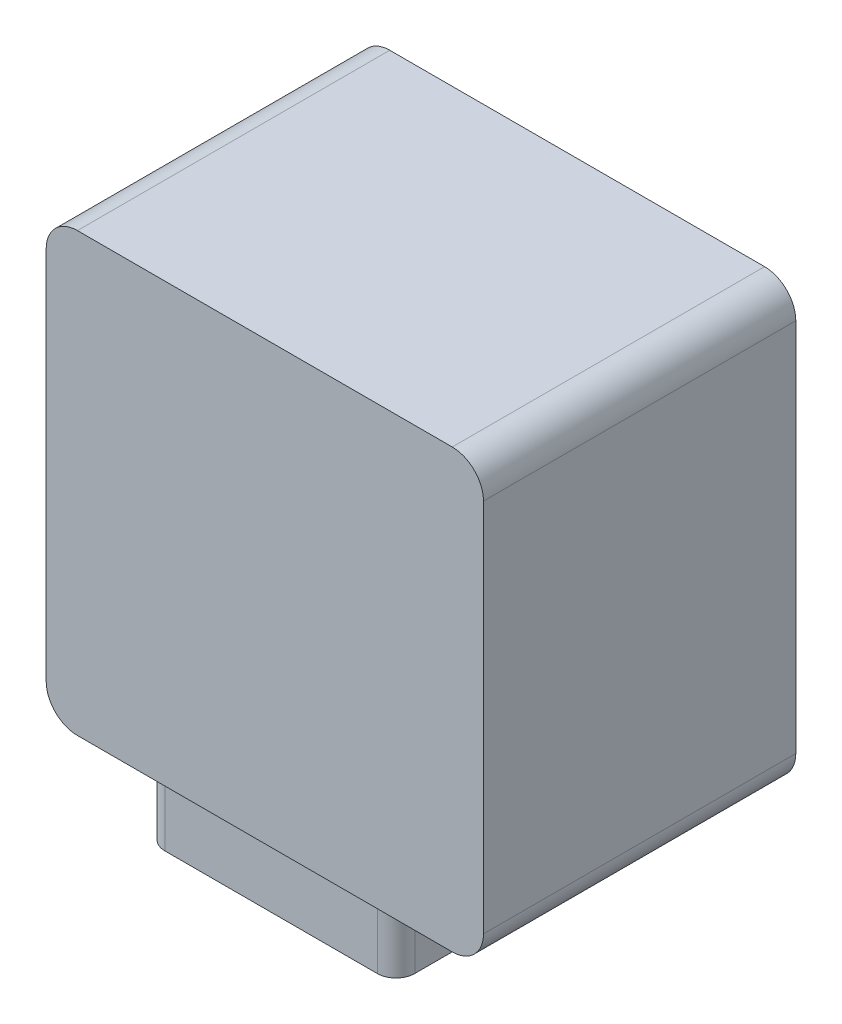
SolidWorks part; units mm, degrees
ref_plane "前视基准面" through (0, 0, 0) normal (0, 0, 1) x (1, 0, 0)
ref_plane "上视基准面" through (0, 0, 0) normal (0, 1, 0) x (1, 0, 0)
ref_plane "右视基准面" through (0, 0, 0) normal (1, 0, 0) x (0, 0, -1)
sketch "草图1" plane through (0, 0, 0) normal (0, 0, 1) x (1, 0, 0)
  line L1 (-48.1935, 66.2876) -> (11.8065, 66.2876)
  line L2 (-53.1935, 61.2876) -> (-53.1935, 1.2876)
  line L3 (-48.1935, -3.7124) -> (11.8065, -3.7124)
  line L4 (16.8065, 61.2876) -> (16.8065, 1.2876)
  line L5 (-53.1935, 66.2876) -> (16.8065, -3.7124) construction
  line L6 (-53.1935, -3.7124) -> (16.8065, 66.2876) construction
  arc A0 (11.8065, 66.2876) -> (16.8065, 61.2876) centre (11.8065, 61.2876) cw
  arc A1 (-48.1935, 66.2876) -> (-53.1935, 61.2876) centre (-48.1935, 61.2876) ccw
  arc A2 (-53.1935, 1.2876) -> (-48.1935, -3.7124) centre (-48.1935, 1.2876) ccw
  arc A3 (11.8065, -3.7124) -> (16.8065, 1.2876) centre (11.8065, 1.2876) ccw
  point P0 (-18.1935, 31.2876)
  dimension "D3" = 5
  dimension "D1" = 70
  dimension "D2" = 70
extrude "凸台-拉伸1" add sketch "草图1" along normal blind 50
sketch "草图2" plane through (0, -3.7124, 0) normal (0, -1, 0) x (1, 0, 0)
  line L0 (-18.1935, 9) -> (-35.1935, 9)
  line L1 (-48.1935, 0) -> (11.8065, 0) construction
  line L2 (-18.1935, 0) -> (-18.1935, 9) construction
  line L3 (-18.1935, 9) -> (-1.1935, 9)
  line L4 (-38.1935, 12) -> (-38.1935, 46)
  line L5 (-35.1935, 49) -> (-1.1935, 49)
  line L6 (1.8065, 46) -> (1.8065, 12)
  circle A0 centre (-18.1935, 29) radius 12.5 construction
  circle A1 centre (-18.1935, 41.5) radius 3
  circle A2 centre (-30.6935, 29) radius 3
  circle A3 centre (-18.1935, 16.5) radius 3
  circle A4 centre (-5.6935, 29) radius 3
  arc A5 (-1.1935, 49) -> (1.8065, 46) centre (-1.1935, 46) cw
  arc A6 (-38.1935, 46) -> (-35.1935, 49) centre (-35.1935, 46) cw
  arc A7 (-35.1935, 9) -> (-38.1935, 12) centre (-35.1935, 12) cw
  arc A8 (-1.1935, 9) -> (1.8065, 12) centre (-1.1935, 12) ccw
  dimension "D1" = 25
  dimension "D2" = 6
  dimension "D3" = 3
extrude "凸台-拉伸2" add sketch "草图2" along normal blind 10
